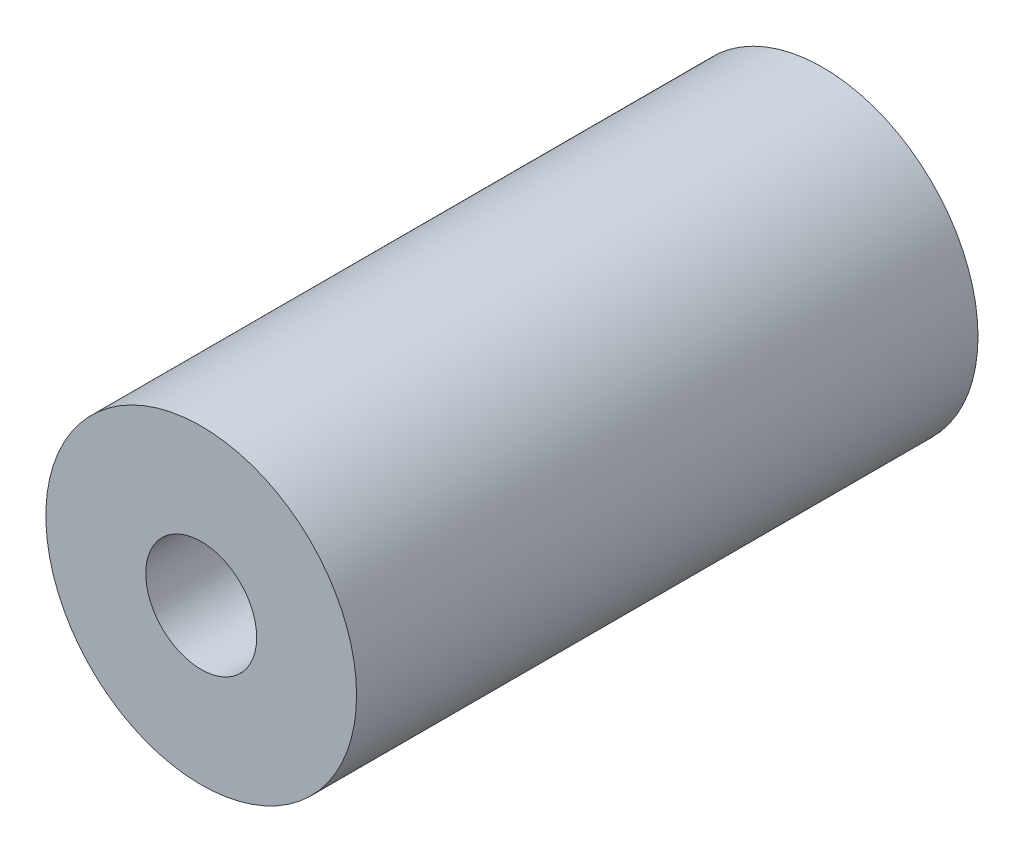
SolidWorks part; units mm, degrees
ref_plane "Front Plane" through (0, 0, 0) normal (0, 0, 1) x (1, 0, 0)
ref_plane "Top Plane" through (0, 0, 0) normal (0, 1, 0) x (1, 0, 0)
ref_plane "Right Plane" through (0, 0, 0) normal (1, 0, 0) x (0, 0, -1)
sketch "Sketch1" plane through (0, 0, 0) normal (0, 0, 1) x (1, 0, 0)
  circle A0 centre (0, 0) radius 1.7
  circle A1 centre (0, 0) radius 4.7625
  dimension "D1" = 3.4
  dimension "D2" = 9.525
extrude "Boss-Extrude1" add sketch "Sketch1" along normal mid plane 19.05
